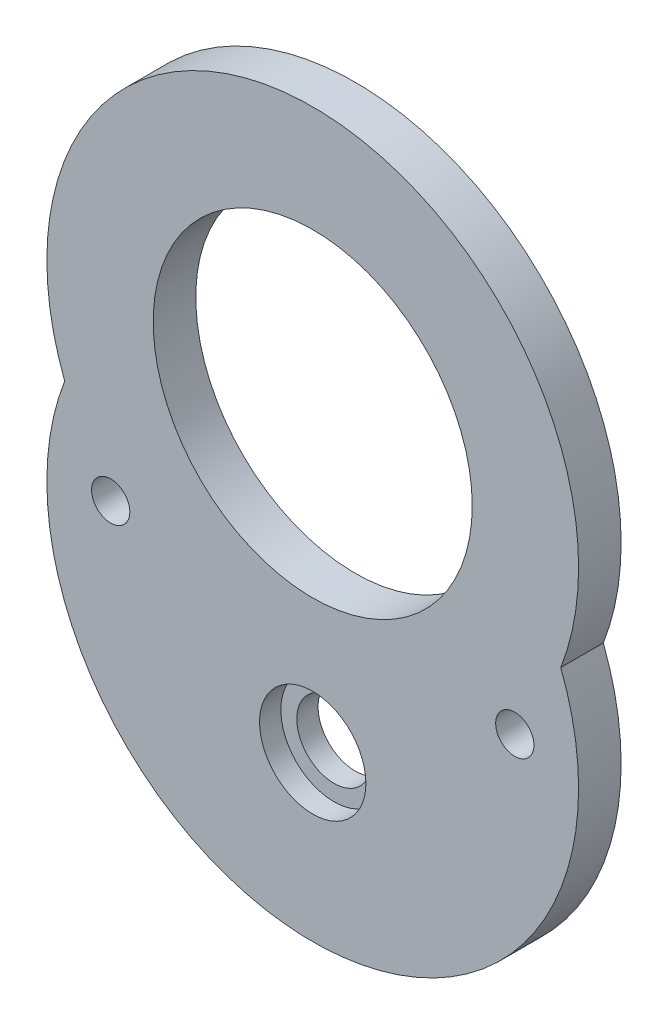
SolidWorks part; units mm, degrees
ref_plane "前视基准面" through (0, 0, 0) normal (0, 0, 1) x (1, 0, 0)
ref_plane "上视基准面" through (0, 0, 0) normal (0, 1, 0) x (1, 0, 0)
ref_plane "右视基准面" through (0, 0, 0) normal (1, 0, 0) x (0, 0, -1)
sketch "草图1" plane through (0, 0, 0) normal (0, 0, 1) x (1, 0, 0)
  line L0 (-14.1154, -21.5) -> (0, -21.5) construction
  line L1 (0, -21.5) -> (0, 0) construction
  line L2 (0, 0) -> (0, 12.5) construction
  line L3 (0, 12.5) -> (-15.5399, 12.5) construction
  arc A0 (11.6619, -4.5) -> (-11.6619, -4.5) centre (0, 0) ccw
  arc A1 (-11.6619, -4.5) -> (11.6619, -4.5) centre (0, -9) ccw
  circle A2 centre (0, 0) radius 7.5
  circle A3 centre (0, -13.8) radius 1.75
  circle A4 centre (-9.5, -8.3) radius 0.9
  circle A5 centre (9.5, -8.3) radius 0.9
  dimension "D1" = 25
  dimension "D2" = 25
  dimension "D4" = 15
  dimension "D5" = 1.8
  dimension "D6" = 19
  dimension "D7" = 8.3
  dimension "D8" = 13.8
  dimension "D9" = 3.5
  dimension "D3" = 34
extrude "凸台-拉伸1" add sketch "草图1" along normal blind 2
cosmetic thread "装饰螺纹线1" parameters "D2"=2.5
cosmetic thread "装饰螺纹线2" parameters "D2"=2.5
sketch "草图2" plane through (0, 0, 2) normal (0, 0, 1) x (1, 0, 0)
  circle A0 centre (0, -13.8) radius 2.5
  dimension "D1" = 5
extrude "切除-拉伸1" cut sketch "草图2" against normal blind 1
